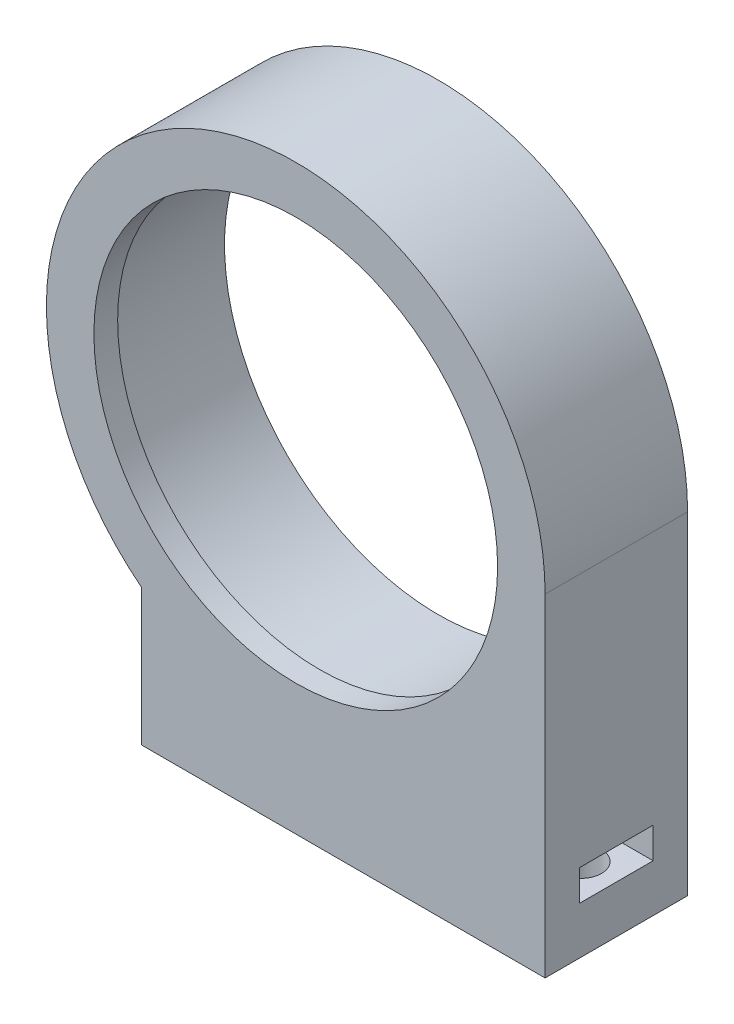
SolidWorks part; units mm, degrees
ref_plane "Alzado" through (0, 0, 0) normal (0, 0, 1) x (1, 0, 0)
ref_plane "Planta" through (0, 0, 0) normal (0, 1, 0) x (1, 0, 0)
ref_plane "Vista lateral" through (0, 0, 0) normal (1, 0, 0) x (0, 0, -1)
sketch "Croquis1" plane through (0, 0, 0) normal (0, 0, 1) x (1, 0, 0)
  line L1 (-13, -28) -> (21, -28)
  line L2 (21, -28) -> (21, 0)
  line L3 (-13, -16.4924) -> (-13, -28)
  circle A0 centre (0, 0) radius 18
  arc A2 (21, 0) -> (-13, -16.4924) centre (0, 0) ccw
  dimension "D1" = 36
  dimension "D2" = 34
  dimension "D3" = 28
extrude "Saliente-Extruir1" add sketch "Croquis1" along normal blind 10
sketch "Croquis2" plane through (0, 0, 10) normal (0, 0, 1) x (1, 0, 0)
  line L0 (21, 0) -> (21, -28)
  line L1 (21, -28) -> (-13, -28)
  line L3 (-13, -28) -> (-13, -16.4924)
  circle A0 centre (0, 0) radius 17
  arc A2 (21, 0) -> (-13, -16.4924) centre (0, 0) ccw
  dimension "D1" = 34
extrude "Saliente-Extruir2" add sketch "Croquis2" along normal blind 2
sketch "Croquis7" plane through (0, -28, 0) normal (0, -1, 0) x (1, 0, 0)
  line L0 (-21, 6) -> (21, 6) construction
  line L2 (21, 12) -> (21, 0) construction
  line L3 (-13, 12) -> (-13, 0) construction
  circle A0 centre (-10, 6) radius 1.75
  circle A1 centre (18, 6) radius 1.75
  dimension "D1" = 3.5
  dimension "D2" = 3.5
  dimension "D3" = 3
  dimension "D4" = 3
extrude "Cortar-Extruir3" cut sketch "Croquis7" against normal blind 8
ref_plane "Plano1" through (0, -24, 0) normal (0, -1, 0) x (-1, 0, 0)
sketch "Croquis8" plane through (0, -24, 0) normal (0, -1, 0) x (-1, 0, 0)
  line L0 (-18, -2.9) -> (-21, -2.9)
  line L1 (-21, -12) -> (-21, 0) construction
  line L2 (-18, -9.1) -> (-21, -9.1)
  line L3 (10, -2.9) -> (13, -2.9)
  line L4 (13, -12) -> (13, 0) construction
  line L5 (13, -12) -> (13, 0) construction
  line L6 (10, -9.1) -> (13, -9.1)
  line L7 (13, -2.9) -> (13, -9.1)
  line L10 (-21, -2.9) -> (-21, -9.1)
  arc A0 (-18, -9.1) -> (-18, -2.9) centre (-18, -6) ccw
  arc A1 (10, -2.9) -> (10, -9.1) centre (10, -6) ccw
  dimension "D1" = 6.2
  dimension "D2" = 6.2
extrude "Cortar-Extruir4" cut sketch "Croquis8" against normal blind 2.6
